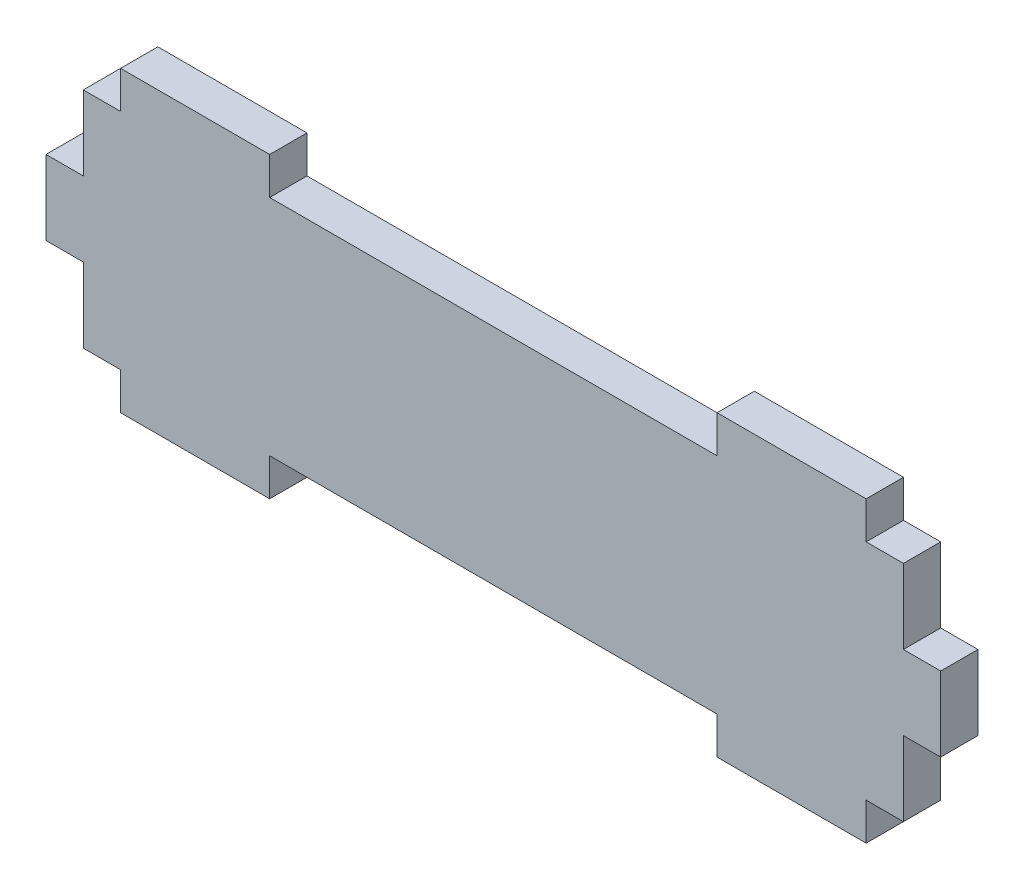
SolidWorks part; units mm, degrees
ref_plane "Front Plane" through (0, 0, 0) normal (0, 0, 1) x (1, 0, 0)
ref_plane "Top Plane" through (0, 0, 0) normal (0, 1, 0) x (1, 0, 0)
ref_plane "Right Plane" through (0, 0, 0) normal (1, 0, 0) x (0, 0, -1)
sketch "Sketch1" plane through (0, 0, 0) normal (0, 0, 1) x (1, 0, 0)
  line L0 (0, 19.05) -> (6.35, 19.05)
  line L1 (6.35, 6.35) -> (12.7, 6.35)
  line L2 (0, 31.75) -> (0, 19.05)
  line L3 (6.35, 44.45) -> (12.7, 44.45)
  line L4 (146.05, 44.45) -> (146.05, 31.75)
  line L5 (12.7, 50.8) -> (38.1, 50.8)
  line L6 (6.35, 44.45) -> (6.35, 31.75)
  line L7 (12.7, 0) -> (38.1, 0)
  line L8 (152.4, 31.75) -> (152.4, 19.05)
  line L9 (0, 31.75) -> (6.35, 31.75)
  line L10 (6.35, 19.05) -> (6.35, 6.35)
  line L11 (146.05, 31.75) -> (152.4, 31.75)
  line L12 (146.05, 19.05) -> (152.4, 19.05)
  line L13 (146.05, 19.05) -> (146.05, 6.35)
  line L14 (12.7, 44.45) -> (12.7, 50.8)
  line L15 (38.1, 44.45) -> (38.1, 50.8)
  line L16 (139.7, 44.45) -> (139.7, 50.8)
  line L17 (114.3, 44.45) -> (114.3, 50.8)
  line L18 (38.1, 44.45) -> (114.3, 44.45)
  line L19 (114.3, 50.8) -> (139.7, 50.8)
  line L20 (139.7, 44.45) -> (146.05, 44.45)
  line L21 (12.7, 6.35) -> (12.7, 0)
  line L22 (38.1, 6.35) -> (38.1, 0)
  line L23 (114.3, 6.35) -> (114.3, 0)
  line L24 (139.7, 6.35) -> (139.7, 0)
  line L25 (38.1, 6.35) -> (114.3, 6.35)
  line L26 (114.3, 0) -> (139.7, 0)
  line L27 (139.7, 6.35) -> (146.05, 6.35)
extrude "Boss-Extrude1" add sketch "Sketch1" along normal blind 6.35
